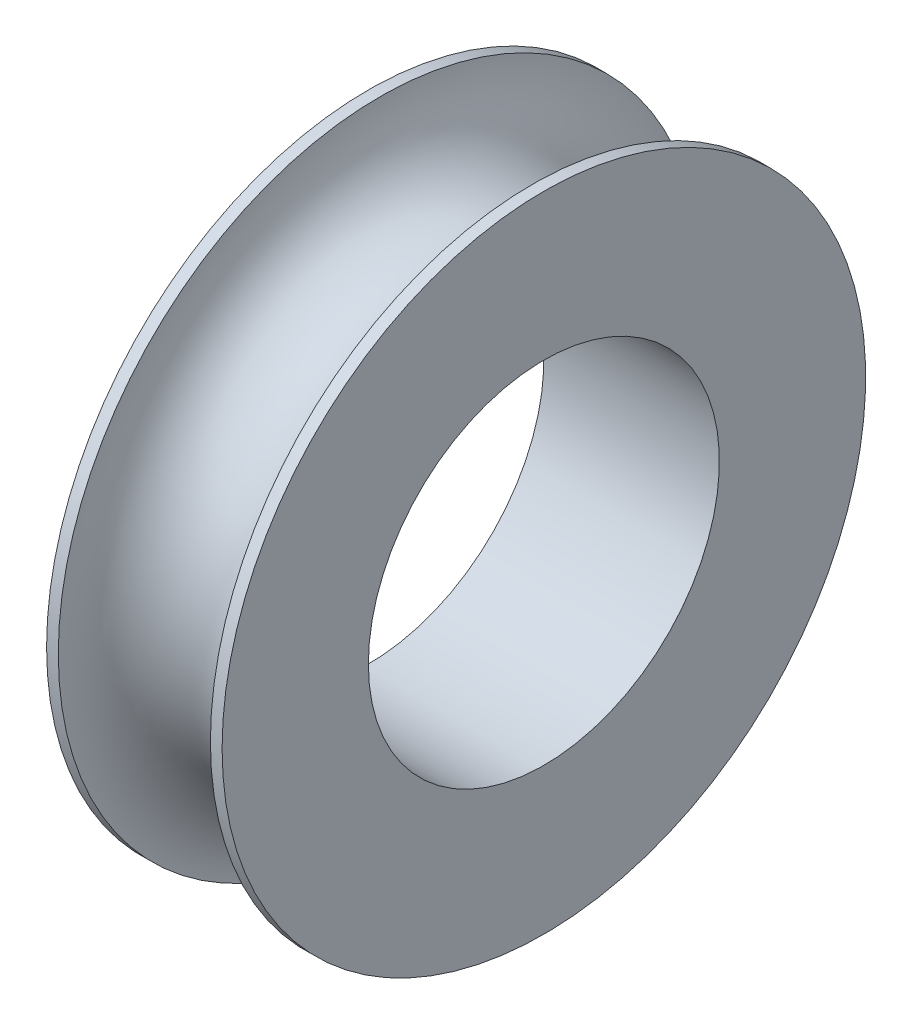
SolidWorks part; units mm, degrees
ref_plane "Front Plane" through (0, 0, 0) normal (0, 0, 1) x (1, 0, 0)
ref_plane "Top Plane" through (0, 0, 0) normal (0, 1, 0) x (1, 0, 0)
ref_plane "Right Plane" through (0, 0, 0) normal (1, 0, 0) x (0, 0, -1)
sketch "Sketch1" plane through (0, 0, 0) normal (0, 1, 0) x (1, 0, 0)
  line L0 (0, 11) -> (0, 6)
  line L1 (0, 11) -> (0.4, 11)
  line L2 (5.6, 11) -> (6, 11)
  line L3 (6, 11) -> (6, 6)
  line L4 (-8.5325, 0) -> (13.2499, 0) construction
  line L5 (0, 6) -> (6, 6)
  arc A0 (0.4, 11) -> (5.6, 11) centre (3, 11) ccw
  dimension "D1" = 2.6
  dimension "D4" = 6
  dimension "D2" = 6
  dimension "D3" = 5
revolve "Revolve1" add sketch "Sketch1" angle 360 about L4
